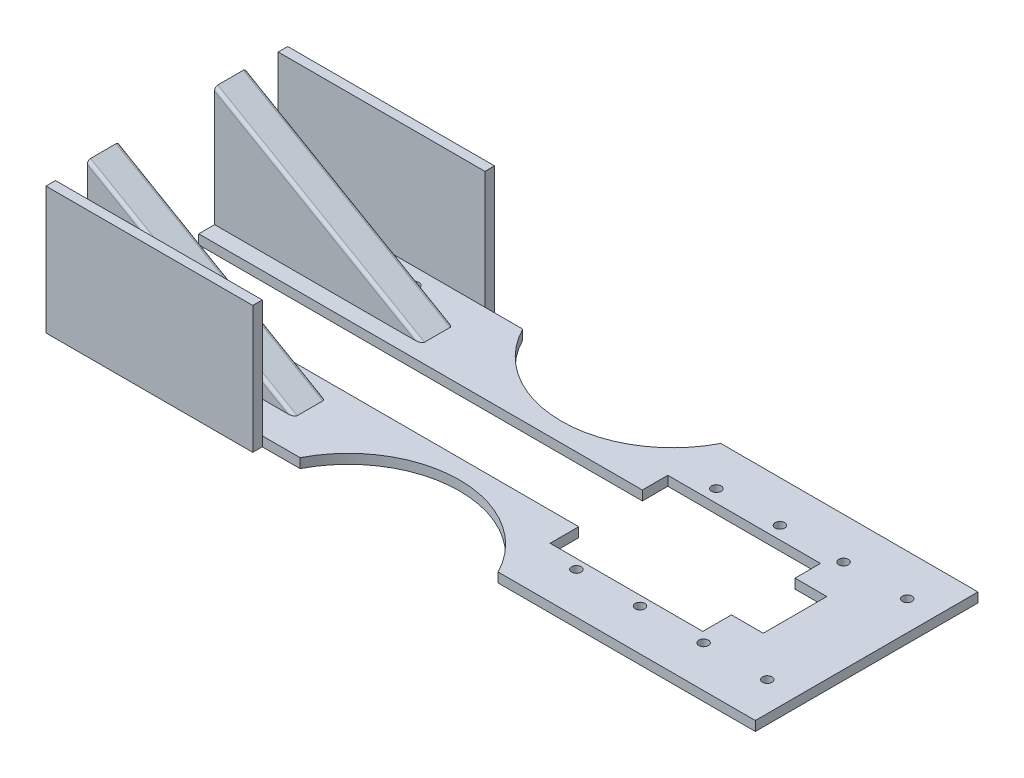
SolidWorks part; units mm, degrees
ref_plane "前视基准面" through (0, 0, 0) normal (0, 0, 1) x (1, 0, 0)
ref_plane "上视基准面" through (0, 0, 0) normal (0, 1, 0) x (1, 0, 0)
ref_plane "右视基准面" through (0, 0, 0) normal (1, 0, 0) x (0, 0, -1)
sketch "草图1" plane through (0, 0, 0) normal (0, 1, 0) x (1, 0, 0)
  line L0 (-92.9537, 0) -> (133.3808, 0) construction
  line L1 (0, 79.573) -> (0, -79.8577) construction
  line L2 (-82.7046, -35) -> (-82.7046, 35)
  line L3 (-82.7046, 35) -> (137.2954, 35)
  line L4 (137.2954, 35) -> (137.2954, -35)
  line L5 (-82.7046, -35) -> (137.2954, -35)
  point P10 (137.2954, 0)
  point P11 (-82.7046, 0)
  dimension "D1" = 70
  dimension "D2" = 220
extrude "凸台-拉伸1" add sketch "草图1" along normal blind 3
sketch "草图2" plane through (0, 0, 0) normal (0, 0, 1) x (1, 0, 0)
  line L0 (-2.7046, 3) -> (-2.7046, 43.2178) construction
  line L2 (59.2954, 3) -> (59.2954, 47.8617) construction
  line L3 (-82.7046, 3) -> (-82.7046, 0) construction
  line L5 (-82.7046, 40.5278) -> (-82.7046, 3)
  line L10 (-82.7046, 3) -> (-17.7046, 3)
  line L11 (-82.7046, 40.5278) -> (-17.7046, 3)
  dimension "D1" = 62
  dimension "D2" = 80
  dimension "D3" = 30
  dimension "D4" = 65
extrude "凸台-拉伸2" add sketch "草图2" along normal blind 25 and the other way blind 25
sketch "草图6" plane through (-82.7046, 0, 0) normal (-1, 0, 0) x (0, 0, 1)
  line L0 (0, 40.5278) -> (0, 0) construction
  line L1 (-25, 40.5278) -> (25, 40.5278) construction
  line L2 (-15, 40.5278) -> (-15, 3)
  line L3 (-15, 3) -> (15, 3)
  line L4 (15, 3) -> (15, 40.5278)
  line L5 (15, 40.5278) -> (-15, 40.5278)
  dimension "D1" = 15
  dimension "D2" = 15
extrude "切除-拉伸4" cut sketch "草图6" against normal through all
ref_plane "基准面1" through (-87.2964, 23.391, 0) normal (-0.9659, 0.2588, 0) x (0, 0, 1)
sketch "草图7" plane through (0, 3, 0) normal (0, 1, 0) x (1, 0, 0)
  line L0 (-2.7046, 35) -> (-2.7046, -35) construction
  line L4 (137.2954, 35) -> (-82.7046, 35) construction
  line L5 (-82.7046, -35) -> (137.2954, -35) construction
  line L6 (-82.7046, 35) -> (-82.7046, 25) construction
  line L7 (53.2954, 35) -> (53.2954, -35) construction
  line L8 (25.2954, 88.1076) -> (25.2954, -100.7895) construction
  line L9 (-82.7046, 0) -> (117.2954, 0) construction
  line L11 (-82.7046, 15) -> (-82.7046, -15) construction
  circle A0 centre (25.2954, 51) radius 35
  circle A1 centre (25.2954, -51) radius 35
  dimension "D4" = 70
  dimension "D1" = 80
  dimension "D2" = 56
  dimension "D3" = 28
  dimension "D5" = 102
extrude "切除-拉伸5" cut sketch "草图7" against normal through all
sketch "草图8" plane through (-82.7046, 0, 0) normal (-1, 0, 0) x (0, 0, 1)
  line L0 (35, 0) -> (35, 40)
  line L1 (35, 40) -> (38, 40)
  line L2 (38, 40) -> (38, 0)
  line L3 (38, 0) -> (35, 0)
  line L4 (0, 36.5043) -> (0, -13.2047) construction
  line L5 (-38, 0) -> (-35, 0)
  line L6 (-38, 40) -> (-38, 0)
  line L7 (-35, 40) -> (-38, 40)
  line L8 (-35, 0) -> (-35, 40)
  dimension "D1" = 3
  dimension "D2" = 40
extrude "凸台-拉伸3" add sketch "草图8" against normal blind 65
sketch "草图9" plane through (0, 3, 0) normal (0, 1, 0) x (1, 0, 0)
  line L0 (-82.7046, 15) -> (-82.7046, -15) construction
  line L1 (-82.7046, 0) -> (117.2954, 0) construction
  circle A0 centre (-74.7668, 29.8601) radius 1.5
  circle A1 centre (-54.7668, 29.8601) radius 1.5
  circle A2 centre (-34.7668, 29.8601) radius 1.5
  circle A3 centre (-34.7668, -29.8601) radius 1.5
  circle A4 centre (-54.7668, -29.8601) radius 1.5
  circle A5 centre (-74.7668, -29.8601) radius 1.5
  circle A12 centre (68.0316, 22) radius 1.5
  circle A13 centre (88.0316, 22) radius 1.5
  circle A14 centre (108.0316, 22) radius 1.5
  circle A15 centre (108.0316, -22) radius 1.5
  circle A16 centre (88.0316, -22) radius 1.5
  circle A17 centre (68.0316, -22) radius 1.5
  circle A18 centre (128.0316, 22) radius 1.5
  circle A19 centre (128.0316, -22) radius 1.5
  dimension "D1" = 3
  dimension "D3" = 22
  dimension "D5" = 3
  dimension "D7" = 3
  dimension "D9" = 3
  dimension "D4" = 20
  dimension "D8" = 20
  dimension "D2" = 3
  dimension "D6" = 3
extrude "切除-拉伸6" cut sketch "草图9" against normal through all
fillet "圆角5" radius 1 4 edges at (-50.2046, 21.7639, -15) (-50.2046, 21.7639, 15) (-50.2046, 21.7639, 25) (-50.2046, 21.7639, -25)
sketch "草图10" plane through (0, 3, 0) normal (0, 1, 0) x (1, 0, 0)
  line L0 (-82.7046, 0) -> (137.2954, 0) construction
  line L1 (-82.7046, 15) -> (-82.7046, -15) construction
  line L2 (137.2954, 35) -> (137.2954, -35) construction
  line L3 (-82.7046, -10) -> (-82.7046, 10)
  line L4 (-82.7046, 10) -> (-17.7046, 10)
  line L5 (-17.7046, 10) -> (-17.7046, -10)
  line L6 (-82.7046, -10) -> (-17.7046, -10)
  point P11 (-17.7046, 0)
  dimension "D1" = 20
extrude "切除-拉伸7" cut sketch "草图10" against normal through all
sketch "草图11" plane through (0, 0, 0) normal (0, 1, 0) x (1, 0, 0)
  line L0 (-17.7046, 10) -> (-17.7046, -10)
  line L1 (-17.7046, -10) -> (114.778, -10)
  line L2 (114.778, -10) -> (114.778, 10)
  line L3 (114.778, 10) -> (-17.7046, 10)
extrude "切除-拉伸8" cut sketch "草图11" along normal blind 25
sketch "草图12" plane through (0, 0, 0) normal (0, 1, 0) x (1, 0, 0)
  line L0 (56.778, 18) -> (56.778, -19)
  line L1 (56.778, -19) -> (104.778, -19)
  line L2 (104.778, -19) -> (104.778, 18)
  line L3 (104.778, 18) -> (56.778, 18)
  line L4 (114.778, 10) -> (-82.7046, 10) construction
  line L5 (-82.7046, -10) -> (114.778, -10) construction
  line L6 (114.778, 10) -> (114.778, -10) construction
  dimension "D1" = 8
  dimension "D2" = 9
  dimension "D3" = 58
  dimension "D4" = 10
extrude "切除-拉伸9" cut sketch "草图12" along normal blind 30
sketch "草图13" plane through (0, 0, 0) normal (0, 1, 0) x (1, 0, 0)
  line L0 (56.778, 16.4709) -> (56.778, -1.0161) construction
  line L1 (56.778, 10) -> (56.778, 18) construction
  line L2 (68.0316, 22) -> (68.0316, -1.0161) construction
  line L3 (88.0316, 22) -> (88.0316, -1.0161) construction
  line L4 (108.0316, 22) -> (108.0316, -1.0161) construction
  line L5 (0, 0) -> (124.4685, 0) construction
